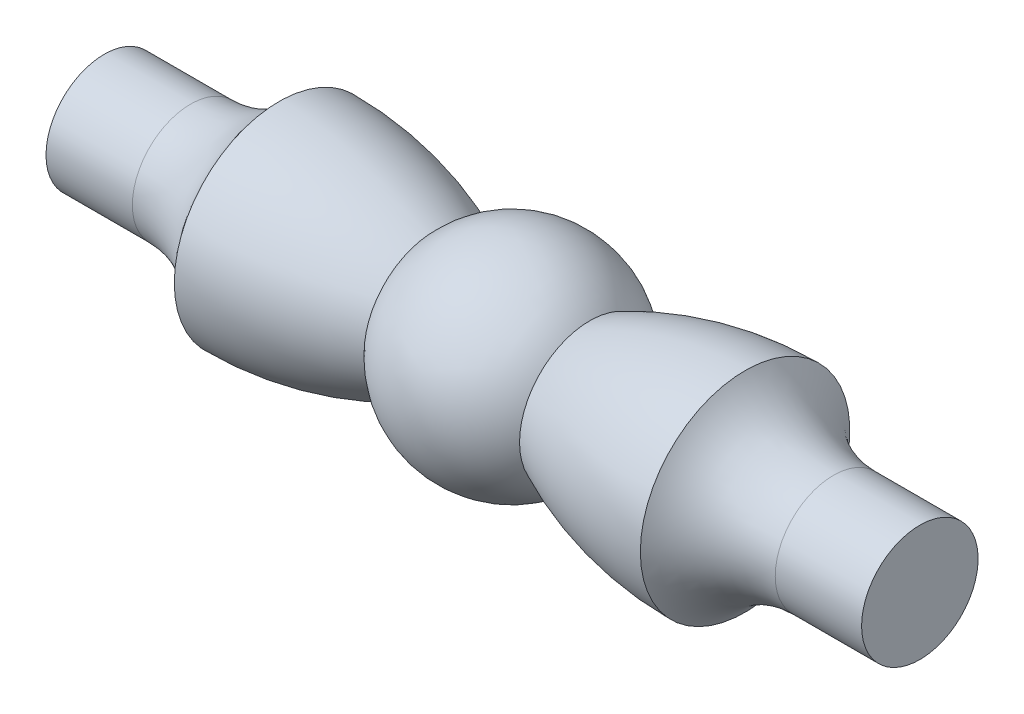
SolidWorks part; units mm, degrees
ref_plane "Face" through (0, 0, 0) normal (0, 0, 1) x (1, 0, 0)
ref_plane "Dessus" through (0, 0, 0) normal (0, 1, 0) x (1, 0, 0)
ref_plane "Droite" through (0, 0, 0) normal (1, 0, 0) x (0, 0, -1)
sketch "Esquisse1" plane through (0, 0, 0) normal (0, 0, 1) x (1, 0, 0)
  line L0 (-7, 0) -> (-7, 1)
  line L1 (-4, 1.798) -> (4, 1.798) construction
  line L3 (-7, 0) -> (7, 0) construction
  line L5 (0, 1.798) -> (0, 14.1211) construction
  line L6 (7, 1) -> (5.5177, 1)
  line L7 (-7, 0) -> (7, 0)
  line L8 (7, 0) -> (7, 1)
  line L11 (-7, 1) -> (-5.5177, 1)
  arc A0 (1.334, 1.2054) -> (4, 1.798) centre (4, -4.4956) cw
  arc A1 (5.5177, 1) -> (4, 1.798) centre (5.5177, 2.8423) cw
  arc A2 (1.334, 1.2054) -> (-1.334, 1.2054) centre (0, 0) ccw
  arc A3 (-5.5177, 1) -> (-4, 1.798) centre (-5.5177, 2.8423) ccw
  arc A4 (-4, 1.798) -> (-1.334, 1.2054) centre (-4, -4.4956) cw
  dimension "D1" = 2
  dimension "D2" = 14
  dimension "D3" = 8
revolve "Révolution1" add sketch "Esquisse1" angle 360 about L7
